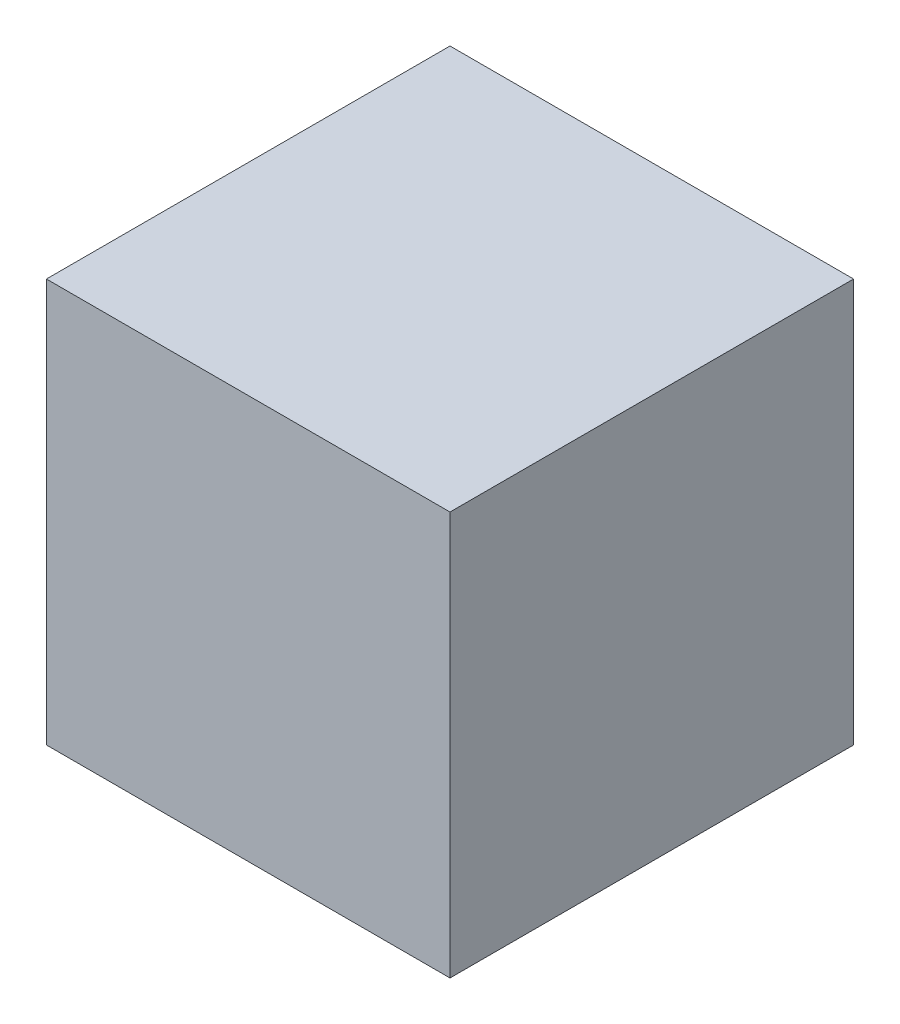
SolidWorks part; units mm, degrees
ref_plane "Front Plane" through (0, 0, 0) normal (0, 0, 1) x (1, 0, 0)
ref_plane "Top Plane" through (0, 0, 0) normal (0, 1, 0) x (1, 0, 0)
ref_plane "Right Plane" through (0, 0, 0) normal (1, 0, 0) x (0, 0, -1)
sketch "Sketch1" plane through (0, 0, 0) normal (0, 0, 1) x (1, 0, 0)
  line L1 (-100, 100) -> (100, 100)
  line L2 (-100, 100) -> (-100, -100)
  line L3 (-100, -100) -> (100, -100)
  line L4 (100, 100) -> (100, -100)
  line L5 (0, -100) -> (0, 100) construction
  line L6 (-100, 0) -> (100, 0) construction
  point P0 (0, 0)
  dimension "D1" = 200
  dimension "D2" = 200
extrude "Boss-Extrude1" add sketch "Sketch1" along normal blind 200
